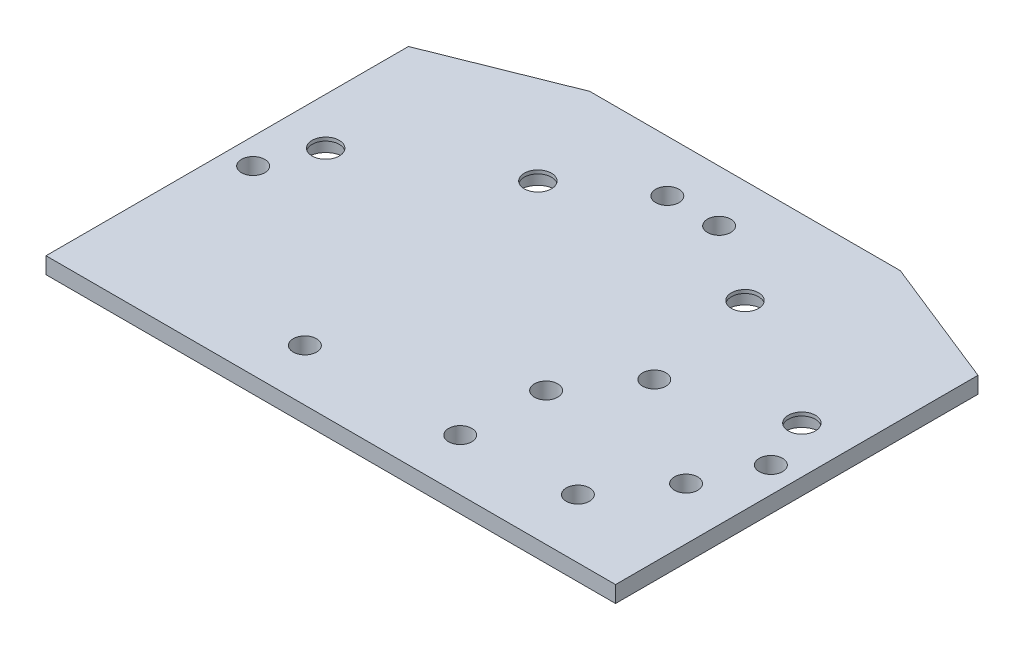
SolidWorks part; units mm, degrees
material "6061-T6 (SS)"
ref_plane "Front Plane" through (0, 0, 0) normal (0, 0, 1) x (1, 0, 0)
ref_plane "Top Plane" through (0, 0, 0) normal (0, 1, 0) x (1, 0, 0)
ref_plane "Right Plane" through (0, 0, 0) normal (1, 0, 0) x (0, 0, -1)
sketch "Sketch1" plane through (0, 0, 0) normal (0, 1, 0) x (1, 0, 0)
  line L0 (-55, 15) -> (-30, 25)
  line L1 (55, -55) -> (-55, -55)
  line L7 (30, 25) -> (55, 15)
  line L8 (-55, -55) -> (-55, 15)
  line L9 (55, -55) -> (55, 15)
  line L10 (30, 25) -> (-30, 25)
  point P0 (0, 0)
  dimension "D1" = 25
  dimension "D2" = 10
  dimension "D3" = 25
  dimension "D4" = 110
  dimension "D5" = 70
  dimension "D6" = 15
  dimension "D7" = 55
extrude "Boss-Extrude1" add sketch "Sketch1" along normal mid plane 3.175 contours L0 L10 L7 L9 L1 L8
sketch "Sketch4" plane through (0, 1.5875, 0) normal (0, 1, 0) x (1, 0, 0)
  line L0 (30, 25) -> (-30, 25) construction
  line L3 (-45.9808, -10) -> (-20, 5)
  line L5 (-55, -55) -> (-55, 15) construction
  point P0 (-20, 5)
  point P2 (20, 5)
  point P4 (45.9808, -10)
  point P6 (-45.9808, -10)
  dimension "D1" = 20
  dimension "D2" = 30
  dimension "D3" = 20
  dimension "D4" = 20
  dimension "D5" = 30
  dimension "D7" = 60
hole_wizard "Ø1.0mm Dowel Hole1" positions "Sketch4" profile "Sketch3" hole size "Ø1.0" standard "ANSI Metric" end condition through all
sketch "Sketch3" plane through (-20, 1.5875, -5) normal (1, 0, 0) x (0, 0, 1)
  line L0 (0, 0) -> (0, 3.175)
  line L1 (0, 3.175) -> (2.625, 3.175)
  line L2 (2.625, 3.175) -> (2.625, 0)
  line L5 (2.625, 0) -> (0, 0)
  line L11 (0, -6.35) -> (0, 107.95) construction
  dimension "Thru Hole Dia." = 5.25
  dimension "Thru Hole Depth" = 3.175
sketch "Sketch6" plane through (0, -1.5875, 0) normal (0, -1, 0) x (1, 0, 0)
  circle A0 centre (-45.9808, 10) radius 3.45
  circle A1 centre (-20, -5) radius 3.45
  circle A2 centre (20, -5) radius 3.45
  circle A3 centre (45.9808, 10) radius 3.45
  dimension "D1" = 6.9
  dimension "D2" = 6.9
  dimension "D3" = 6.9
  dimension "D4" = 6.9
extrude "Cut-Extrude2" cut sketch "Sketch6" against normal blind 2.5
sketch "Sketch9" plane through (0, -1.5875, 0) normal (0, -1, 0) x (-1, 0, 0)
  line L0 (-44.9191, -31.301) -> (-15.8366, -29.2489) construction
  line L2 (-36.3154, -43.5883) -> (-24.4403, -16.9616) construction
  line L3 (-30.3779, -30.275) -> (20, 5) construction
  line L5 (-24.4403, -16.9616) -> (-20.1385, -23.1052) construction
  line L6 (-20.1385, -23.1052) -> (-15.8366, -29.2489) construction
  line L8 (-30, 25) -> (30, 25) construction
  point P0 (-24.4403, -16.9616)
  point P2 (-15.8366, -29.2489)
  point P4 (-44.9191, -31.301)
  point P6 (-36.3154, -43.5883)
  dimension "D1" = 25
  dimension "D2" = 25
  dimension "D3" = 15
  dimension "D4" = 15
  dimension "D5" = 35
  dimension "D6" = 61.5
hole_wizard "M4 Clearance Hole1" positions "Sketch9" profile "Sketch8" hole size "M4" standard "ANSI Metric" end condition through all
sketch "Sketch8" plane through (24.4403, -1.5875, 16.9616) normal (1, 0, 0) x (0, 0, -1)
  line L0 (0, 0) -> (0, 3.175)
  line L1 (0, 3.175) -> (2.25, 3.175)
  line L2 (2.25, 3.175) -> (2.25, 0)
  line L5 (2.25, 0) -> (0, 0)
  line L11 (0, -6.35) -> (0, 107.95) construction
  dimension "Thru Hole Dia." = 4.5
  dimension "Thru Hole Depth" = 3.175
sketch "Sketch13" plane through (0, -1.5875, 0) normal (0, -1, 0) x (-1, 0, 0)
  line L0 (-30, 25) -> (30, 25) construction
  point P0 (-5, 15)
  point P2 (5, 15)
  point P5 (0, 0)
  dimension "D1" = 10
  dimension "D2" = 5
  dimension "D3" = 10
hole_wizard "M4 Clearance Hole2" positions "Sketch13" profile "Sketch11" hole size "M4" standard "ANSI Metric" end condition through all
sketch "Sketch11" plane through (5, -1.5875, -15) normal (1, 0, 0) x (0, 0, -1)
  line L0 (0, 0) -> (0, 3.175)
  line L1 (0, 3.175) -> (2.25, 3.175)
  line L2 (2.25, 3.175) -> (2.25, 0)
  line L5 (2.25, 0) -> (0, 0)
  line L11 (0, -6.35) -> (0, 107.95) construction
  dimension "Thru Hole Dia." = 4.5
  dimension "Thru Hole Depth" = 3.175
sketch "Sketch16" plane through (0, 1.5875, 0) normal (0, 1, 0) x (1, 0, 0)
  line L0 (55, -55) -> (-55, -55) construction
  point P0 (-15, -45)
  point P2 (15, -45)
  point P5 (0, 0)
  dimension "D1" = 10
  dimension "D2" = 15
  dimension "D3" = 15
hole_wizard "M4 Clearance Hole3" positions "Sketch16" profile "Sketch15" hole size "M4" standard "ANSI Metric" end condition through all
sketch "Sketch15" plane through (-15, 1.5875, 45) normal (1, 0, 0) x (0, 0, 1)
  line L0 (0, 0) -> (0, 3.175)
  line L1 (0, 3.175) -> (2.25, 3.175)
  line L2 (2.25, 3.175) -> (2.25, 0)
  line L5 (2.25, 0) -> (0, 0)
  line L11 (0, -6.35) -> (0, 107.95) construction
  dimension "Thru Hole Dia." = 4.5
  dimension "Thru Hole Depth" = 3.175
sketch "Sketch19" plane through (0, 1.5875, 0) normal (0, 1, 0) x (1, 0, 0)
  line L0 (-55, -55) -> (-55, 15) construction
  line L1 (55, -55) -> (55, 15) construction
  line L2 (55, -55) -> (-55, -55) construction
  point P0 (50, -20)
  point P2 (-50, -20)
  dimension "D1" = 5
  dimension "D2" = 5
  dimension "D3" = 35
hole_wizard "M4 Clearance Hole4" positions "Sketch19" profile "Sketch18" hole size "M4" standard "ANSI Metric" end condition through all
sketch "Sketch18" plane through (50, 1.5875, 20) normal (1, 0, 0) x (0, 0, 1)
  line L0 (0, 0) -> (0, 3.175)
  line L1 (0, 3.175) -> (2.25, 3.175)
  line L2 (2.25, 3.175) -> (2.25, 0)
  line L5 (2.25, 0) -> (0, 0)
  line L11 (0, -6.35) -> (0, 107.95) construction
  dimension "Thru Hole Dia." = 4.5
  dimension "Thru Hole Depth" = 3.175
